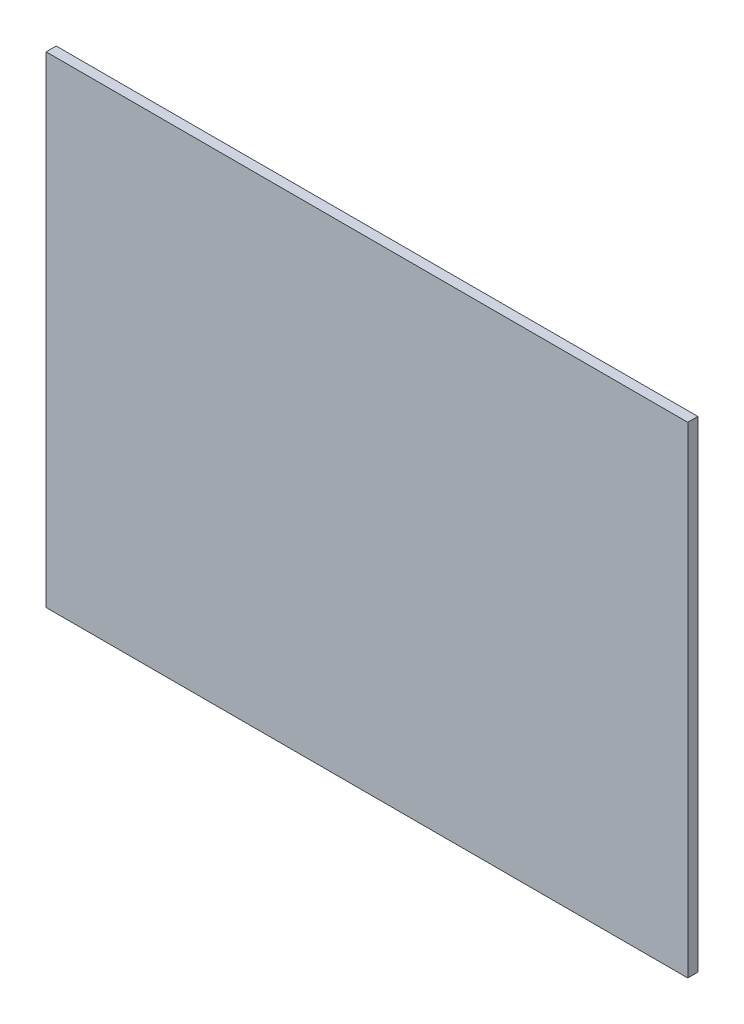
SolidWorks part; units mm, degrees
ref_plane "Front Plane" through (0, 0, 0) normal (0, 0, 1) x (1, 0, 0)
ref_plane "Top Plane" through (0, 0, 0) normal (0, 1, 0) x (1, 0, 0)
ref_plane "Right Plane" through (0, 0, 0) normal (1, 0, 0) x (0, 0, -1)
sketch "Sketch1" plane through (0, 0, 0) normal (0, 0, 1) x (1, 0, 0)
  line L1 (12.7, 9.525) -> (-12.7, 9.525)
  line L2 (12.7, 9.525) -> (12.7, -9.525)
  line L3 (12.7, -9.525) -> (-12.7, -9.525)
  line L4 (-12.7, 9.525) -> (-12.7, -9.525)
  line L5 (12.7, 9.525) -> (-12.7, -9.525) construction
  line L6 (12.7, -9.525) -> (-12.7, 9.525) construction
  point P0 (0, 0)
  dimension "D1" = 19.05
  dimension "D2" = 25.4
extrude "Boss-Extrude1" add sketch "Sketch1" along normal blind 0.4
